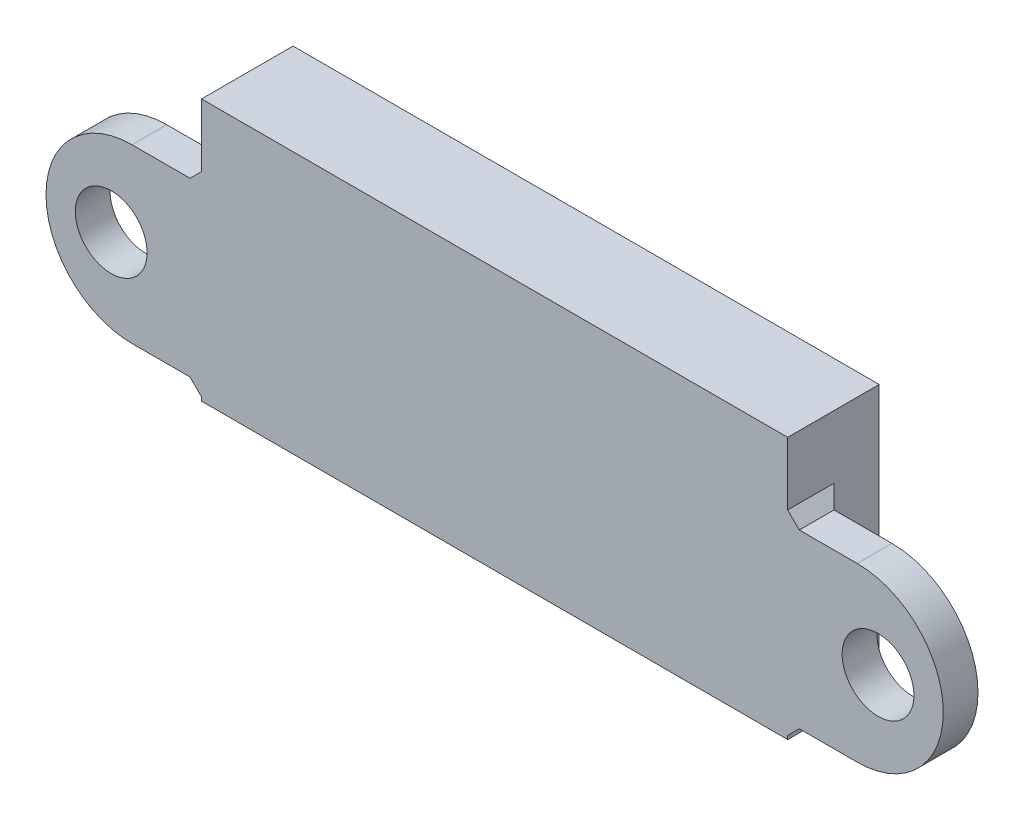
SolidWorks part; units mm, degrees
ref_plane "Front Plane" through (0, 0, 0) normal (0, 0, 1) x (1, 0, 0)
ref_plane "Top Plane" through (0, 0, 0) normal (0, 1, 0) x (1, 0, 0)
ref_plane "Right Plane" through (0, 0, 0) normal (1, 0, 0) x (0, 0, -1)
sketch "Sketch1" plane through (0, 0, 0) normal (0, 0, 1) x (1, 0, 0)
  line L12 (24, 12.55) -> (6.08, 12.55)
  line L13 (6.08, 12.55) -> (-6.08, 12.55)
  line L14 (-6.08, 12.55) -> (-24, 12.55)
  line L15 (-24, 12.55) -> (-24, -7.45)
  line L16 (-24, -7.45) -> (24, -7.45)
  line L17 (24, -7.45) -> (24, 12.55)
  line L18 (24, 12.55) -> (6.08, 12.55)
  line L19 (6.08, 12.55) -> (-6.08, 12.55)
  line L20 (-6.08, 12.55) -> (-24, 12.55)
  line L21 (-24, 12.55) -> (-24, -7.45)
  line L22 (-24, -7.45) -> (24, -7.45)
  line L23 (24, -7.45) -> (24, 12.55)
  dimension "D1" = 0
extrude "Boss-Extrude1" add sketch "Sketch1" along normal blind 5
sketch "Sketch2" plane through (0, 0, 5) normal (0, 0, 1) x (1, 0, 0)
  line L4 (25.3, -8.75) -> (25.3, 13.85)
  line L5 (25.3, 13.85) -> (-25.3, 13.85)
  line L6 (-25.3, 13.85) -> (-25.3, -8.75)
  line L7 (-25.3, -8.75) -> (25.3, -8.75)
  line L8 (24, -7.45) -> (24, 12.55)
  line L9 (24, 12.55) -> (-24, 12.55)
  line L10 (-24, 12.55) -> (-24, -7.45)
  line L11 (-24, -7.45) -> (24, -7.45)
  line L12 (24, -7.45) -> (24, 12.55)
  line L13 (24, 12.55) -> (-24, 12.55)
  line L14 (-24, 12.55) -> (-24, -7.45)
  line L15 (-24, -7.45) -> (24, -7.45)
  dimension "D1" = 0
  dimension "D2" = 1.3
extrude "Boss-Extrude2" add sketch "Sketch2" against normal offset from surface (7.9 mm away) 0.1
sketch "Sketch3" plane through (0, 0, 0) normal (0, 0, -1) x (-1, 0, 0)
  circle A0 centre (-18.5, 0) radius 1.1
  circle A1 centre (18.5, 0) radius 1.1
  dimension "D1" = 2.2
  dimension "D2" = 2.2
extrude "Cut-Extrude1" cut sketch "Sketch3" against normal offset from surface (3 mm away) 2 up to face at (0, 2.55, 5)
sketch "Sketch4" plane through (0, 0, 5) normal (0, 0, 1) x (1, 0, 0)
  line L0 (25.3, -7.4396) -> (31.3, -7.4396)
  line L1 (25.3, 13.85) -> (25.3, -8.75) construction
  line L2 (0, -1008.75) -> (0, 48991.25) construction
  line L3 (31.3, 7.4204) -> (25.3, 7.4204)
  line L4 (25.3, 7.4204) -> (25.3, -7.4396)
  line L5 (25.3, -8.75) -> (-25.3, -8.75) construction
  line L6 (-25.3, -7.4396) -> (-31.3, -7.4396)
  line L7 (-25.3, 7.4204) -> (-25.3, -7.4396)
  line L8 (-31.3, 7.4204) -> (-25.3, 7.4204)
  arc A0 (31.3, -7.4396) -> (31.3, 7.4204) centre (31.3, -0.0096) ccw
  arc A1 (-31.3, -7.4396) -> (-31.3, 7.4204) centre (-31.3, -0.0096) cw
  point P15 (0, -8.75)
  dimension "D1" = 6
  dimension "D2" = 1.3104
  dimension "D3" = 14.86
extrude "Boss-Extrude3" add sketch "Sketch4" against normal blind 3
chamfer "Chamfer1" distance 1 angle 45 6 edges at (25.3, 7.4204, 3.5) (25.3, -0.0096, 2) (25.3, -7.4396, 3.5) (-25.3, 7.4204, 3.5) (-25.3, -0.0096, 2) (-25.3, -7.4396, 3.5)
sketch "Sketch5" plane through (0, 0, 2) normal (0, 0, -1) x (-1, 0, 0)
  line L0 (-968.7, -0.0096) -> (49031.3, -0.0096) construction
  line L2 (0, -1008.75) -> (0, 48991.25) construction
  line L3 (-25.3, -8.75) -> (25.3, -8.75) construction
  circle A2 centre (-33.1, -0.0096) radius 3.1
  circle A3 centre (33.1, -0.0096) radius 3.1
  point P0 (31.3, -0.0096)
  point P15 (0, -8.75)
  dimension "D1" = 6.2
  dimension "D2" = 1.8
extrude "Cut-Extrude2" cut sketch "Sketch5" against normal blind 3
